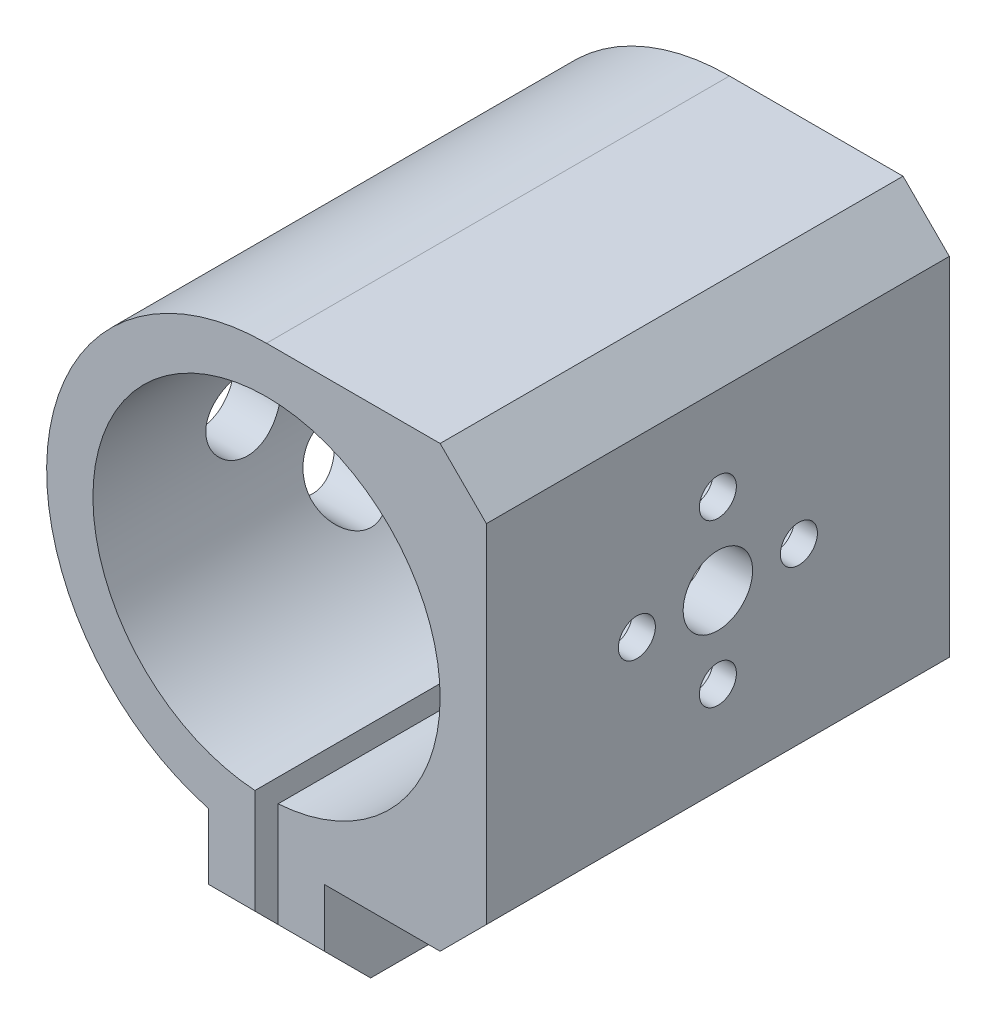
SolidWorks part; units mm, degrees
material "ABS"
ref_plane "前基準面" through (0, 0, 0) normal (0, 0, 1) x (1, 0, 0)
ref_plane "上基準面" through (0, 0, 0) normal (0, 1, 0) x (1, 0, 0)
ref_plane "右基準面" through (0, 0, 0) normal (1, 0, 0) x (0, 0, -1)
sketch "草圖1" plane through (0, 0, 0) normal (0, 0, 1) x (1, 0, 0)
  line L0 (0, 19) -> (19, 19)
  line L1 (19, 19) -> (19, -19)
  line L2 (19, -19) -> (0, -19)
  arc A0 (0, 19) -> (0, -19) centre (0, 0) ccw
  dimension "D1" = 19
  dimension "D2" = 38
  dimension "D3" = 19
extrude "填料-伸長1" add sketch "草圖1" along normal blind 40
sketch "草圖2" plane through (0, 0, 40) normal (0, 0, 1) x (1, 0, 0)
  line L1 (-5, -28) -> (5, -28)
  line L2 (-5, -28) -> (-5, 0)
  line L3 (-5, 0) -> (5, 0)
  line L4 (5, -28) -> (5, 0)
  line L5 (-5, -28) -> (5, 0) construction
  line L6 (-5, 0) -> (5, -28) construction
  point P0 (0, -14)
  point P5 (0, 0)
  dimension "D1" = 28
  dimension "D2" = 10
extrude "填料-伸長2" add sketch "草圖2" against normal blind 15
sketch "草圖3" plane through (0, 0, 40) normal (0, 0, 1) x (1, 0, 0)
  circle A0 centre (0, 0) radius 15
  dimension "D1" = 30
extrude "除料-伸長1" cut sketch "草圖3" against normal up to next
sketch "草圖4" plane through (0, 0, 0) normal (0, 0, -1) x (-1, 0, 0)
  line L1 (-7, 16) -> (7, 16)
  line L2 (-7, 16) -> (-7, 12)
  line L3 (-7, 12) -> (7, 12)
  line L4 (7, 16) -> (7, 12)
  point P4 (0, 16)
  dimension "D1" = 14
  dimension "D2" = 16
  dimension "D3" = 4
extrude "除料-伸長2" cut sketch "草圖4" against normal blind 20
sketch "草圖5" plane through (0, 0, 0) normal (0, 0, -1) x (-1, 0, 0)
  line L1 (-1, -30) -> (1, -30)
  line L2 (-1, -30) -> (-1, 0)
  line L3 (-1, 0) -> (1, 0)
  line L4 (1, -30) -> (1, 0)
  line L5 (-1, -30) -> (1, 0) construction
  line L6 (-1, 0) -> (1, -30) construction
  point P0 (0, -15)
  point P5 (0, 0)
  dimension "D1" = 2
  dimension "D2" = 30
extrude "除料-伸長3" cut sketch "草圖5" against normal up to next
sketch "草圖6" plane through (0, -19, 0) normal (0, -1, 0) x (-1, 0, 0)
  line L0 (0, -40) -> (19, -40) construction
  circle A0 centre (0, -6) radius 11
  dimension "D1" = 22
  dimension "D2" = 34
  dimension "D3" = 18.925
extrude "除料-伸長4" cut sketch "草圖6" against normal blind 20
sketch "草圖7" plane through (19, 0, 0) normal (1, 0, 0) x (0, 0, -1)
  line L0 (-40, 19) -> (0, 19) construction
  line L1 (0, -19) -> (0, 19) construction
  circle A0 centre (-20, 0) radius 3
  point P5 (-20, 19)
  point P9 (0, 0)
  dimension "D1" = 6
extrude "除料-伸長5" cut sketch "草圖7" against normal through all
ref_plane "平面1" through (17, 0, 0) normal (1, 0, 0) x (0, 0, -1)
sketch "草圖14" plane through (19, 0, 0) normal (1, 0, 0) x (0, 0, -1)
  line L0 (-40, 19) -> (0, 19) construction
  circle A0 centre (-20, 7) radius 1.6
  circle A1 centre (-20, 0) radius 3 construction
  point P7 (-20, 19)
  dimension "D1" = 3.2
  dimension "D2" = 7
extrude "除料-伸長6" cut sketch "草圖14" against normal blind 10
sketch "草圖15" plane through (17, 0, 0) normal (1, 0, 0) x (0, 0, -1)
  circle A0 centre (-20, 7) radius 3.25
  dimension "D1" = 6.5
extrude "除料-伸長7" cut sketch "草圖15" against normal through all
pattern_circular "環狀複製排列1" count 4 over 360 about axis through (0, 0, 20) along (1, 0, 0) of "除料-伸長7", "除料-伸長6"
chamfer "導角1" distance 4 angle 45 6 edges at (19, -19, 20) (19, 19, 20) (3, -28, 25) (-3, -28, 25) (-3, -28, 40) (3, -28, 40)
sketch "草圖16" plane through (-5, 0, 0) normal (-1, 0, 0) x (0, 0, 1)
  line L0 (29, -28) -> (36, -28) construction
  line L2 (29, -28) -> (36, -28) construction
  circle A0 centre (32.5, -23) radius 2.25
  point P5 (32.5, -28)
  dimension "D1" = 4.5
  dimension "D2" = 5
extrude "除料-伸長8" cut sketch "草圖16" against normal through all
sketch "草圖17" plane through (0, -19, 0) normal (0, -1, 0) x (-1, 0, 0)
  line L0 (-11, 6.2) -> (11, 6.2)
  line L1 (-11, 6.2) -> (-11, -6.2)
  line L2 (11, 6.2) -> (11, -6.2)
  line L3 (-11, -6.2) -> (11, -6.2)
  line L4 (-11, 6.2) -> (11, -6.2) construction
  line L5 (11, 6.2) -> (-11, -6.2) construction
  point P1 (0, 0)
  dimension "D1" = 22
  dimension "D2" = 12.4
extrude "除料-伸長10" cut sketch "草圖17" against normal blind 10
